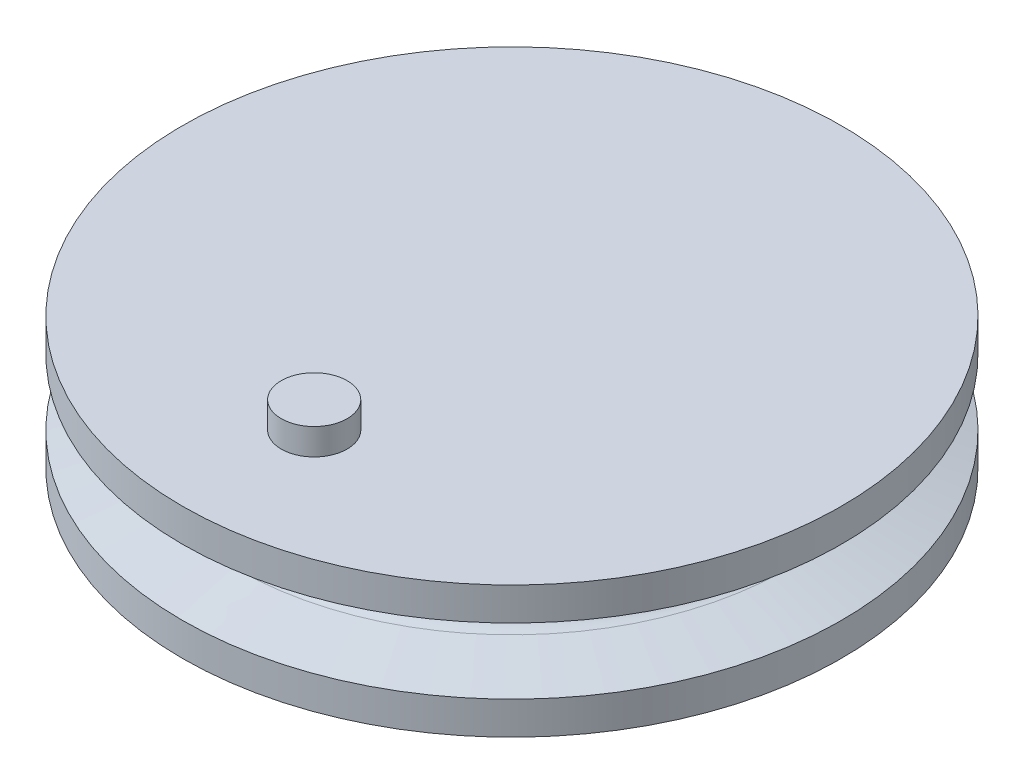
SolidWorks part; units mm, degrees
ref_plane "Front Plane" through (0, 0, 0) normal (0, 0, 1) x (1, 0, 0)
ref_plane "Top Plane" through (0, 0, 0) normal (0, 1, 0) x (1, 0, 0)
ref_plane "Right Plane" through (0, 0, 0) normal (1, 0, 0) x (0, 0, -1)
sketch "Sketch1" plane through (0, 0, 0) normal (0, 1, 0) x (1, 0, 0)
  circle A0 centre (0, 0) radius 20
  dimension "D1" = 40
extrude "Boss-Extrude1" add sketch "Sketch1" along normal blind 10
ref_axis "Axis1" through (0, 10, 0) along (0, -1, 0)
sketch "Sketch2" plane through (0, 0, 0) normal (1, 0, 0) x (0, 0, -1)
  line L0 (20, 0) -> (20, 10) construction
  line L1 (20, 10) -> (25, 10)
  line L2 (25, 10) -> (25, 7.5)
  line L3 (25, 7.5) -> (20.8723, 6.1916)
  line L4 (20, 0) -> (25, 0)
  line L5 (25, 0) -> (25, 2.5)
  line L6 (25, 2.5) -> (20.8723, 3.8084)
  line L7 (21.25, 10) -> (21.25, 0) construction
  line L8 (20, 10) -> (19.25, 10)
  line L9 (20, 10) -> (-20, 10) construction
  line L10 (19.25, 10) -> (19.25, 0)
  line L11 (-20, 0) -> (20, 0) construction
  line L12 (19.25, 0) -> (20, 0)
  arc A0 (20.8723, 6.1916) -> (20.8723, 3.8084) centre (21.25, 5) ccw
  dimension "D1" = 2.5
  dimension "D2" = 2.5
  dimension "D3" = 5
  dimension "D4" = 2
revolve "Revolve1" add sketch "Sketch2" angle 360 about axis through (0, 10, 0) along (0, -1, 0)
sketch "Sketch3" plane through (0, 0, 0) normal (0, -1, 0) x (1, 0, 0)
  circle A0 centre (0, 0) radius 2.5
  dimension "D1" = 5
extrude "Cut-Extrude1" cut sketch "Sketch3" against normal blind 5
sketch "Sketch4" plane through (0, 10, 0) normal (0, 1, 0) x (1, 0, 0)
  line L0 (0, 0) -> (0, -15) construction
  circle A0 centre (0, -15) radius 2.5
  dimension "D1" = 15
  dimension "D2" = 5
extrude "Boss-Extrude2" add sketch "Sketch4" along normal blind 2
